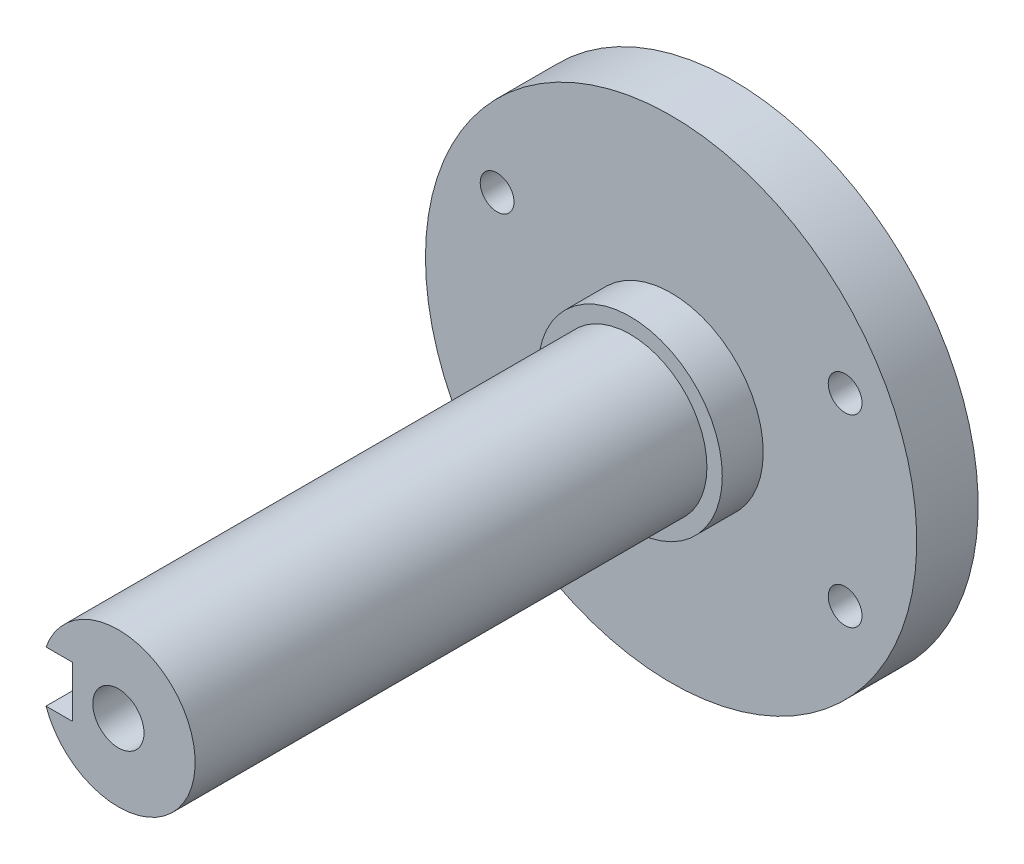
SolidWorks part; units mm, degrees
material "Alumine"
ref_plane "Plan de face" through (0, 0, 0) normal (0, 0, 1) x (1, 0, 0)
ref_plane "Plan de dessus" through (0, 0, 0) normal (0, 1, 0) x (1, 0, 0)
ref_plane "Plan de droite" through (0, 0, 0) normal (1, 0, 0) x (0, 0, -1)
sketch "Esquisse1" plane through (0, 0, 0) normal (0, 0, 1) x (1, 0, 0)
  circle A0 centre (0, 0) radius 9
  dimension "D1" = 18
extrude "Boss.-Extru.1" add sketch "Esquisse1" along normal blind 4
sketch "Esquisse2" plane through (0, 0, 0) normal (0, 0, -1) x (-1, 0, 0)
  circle A0 centre (0, 0) radius 24
  dimension "D1" = 48
extrude "Boss.-Extru.2" add sketch "Esquisse2" along normal blind 6
sketch "Esquisse7" plane through (0, 0, 4) normal (0, 0, 1) x (1, 0, 0)
  circle A0 centre (0, 0) radius 7.5
  dimension "D1" = 15
extrude "Boss.-Extru.3" add sketch "Esquisse7" along normal blind 50
sketch "Esquisse9" plane through (0, 0, 54) normal (0, 0, 1) x (1, 0, 0)
  circle A0 centre (0, 0) radius 7.5
  dimension "D1" = 15
hole_wizard "Trou pour taraudage pour trou taraudé M42" positions "Esquisse5" profile "Esquisse6" hole size "M4" standard "ISO"
sketch "Esquisse5" plane through (0, 0, -6) normal (0, 0, -1) x (-1, 0, 0)
  line L6 (17, -9) -> (-17, -9) construction
  line L7 (17, -9) -> (17, 9) construction
  line L8 (17, 9) -> (-17, 9) construction
  line L9 (-17, -9) -> (-17, 9) construction
  line L10 (17, -9) -> (-17, 9) construction
  line L11 (17, 9) -> (-17, -9) construction
  point P50 (-17, 9)
  point P107 (17, -9)
  point P108 (17, 9)
  point P109 (-17, -9)
  dimension "D1" = 34
  dimension "D2" = 18
sketch "Esquisse6" plane through (17, 9, -6) normal (1, 0, 0) x (0, 1, 0)
  line L0 (0, 0) -> (0, 6.9914)
  line L1 (0, 6.9914) -> (1.65, 6)
  line L2 (1.65, 6) -> (1.65, 0)
  line L5 (1.65, 0) -> (0, 0)
  line L10 (0, 6.9914) -> (-1.65, 6) construction
  line L11 (0, -6.35) -> (0, 107.95) construction
  dimension "Diamètre du perçage" = 3.3
  dimension "Profondeur du perçage" = 6
  dimension "Angle de pointe" = 118
ref_plane "Plan1" through (8.5, 0, 0) normal (1, 0, 0) x (0, 0, -1)
ref_plane "Plan2" through (-7.5, 0, 0) normal (-1, 0, 0) x (0, 0, 1)
sketch "Esquisse10" plane through (-7.5, 0, 0) normal (-1, 0, 0) x (0, 0, 1)
  line L0 (79, 0) -> (29, 0) construction
  line L1 (54, -7.5) -> (54, 7.5) construction
  line L2 (79, -2.5) -> (29, -2.5)
  line L3 (79, 2.5) -> (29, 2.5)
  arc A0 (79, -2.5) -> (79, 2.5) centre (79, 0) ccw
  arc A1 (29, 2.5) -> (29, -2.5) centre (29, 0) ccw
  point P5 (54, 0)
  dimension "D2" = 25
  dimension "D1" = 5
extrude "Enlèv. mat.-Extru.1" cut sketch "Esquisse10" against normal blind 3
hole_wizard "Trou pour taraudage pour trou taraudé M61" positions "Esquisse13" profile "Esquisse12" hole size "M6" standard "ISO"
sketch "Esquisse13" plane through (0, 0, 54) normal (0, 0, 1) x (1, 0, 0)
  point P0 (0, 0)
sketch "Esquisse12" plane through (0, 0, 54) normal (1, 0, 0) x (0, -1, 0)
  line L0 (0, 0) -> (0, 16.5022)
  line L1 (0, 16.5022) -> (2.5, 15)
  line L2 (2.5, 15) -> (2.5, 0)
  line L5 (2.5, 0) -> (0, 0)
  line L10 (0, 16.5022) -> (-2.5, 15) construction
  line L11 (0, -6.35) -> (0, 107.95) construction
  dimension "Diamètre du perçage" = 5
  dimension "Profondeur du perçage" = 15
  dimension "Angle de pointe" = 118
